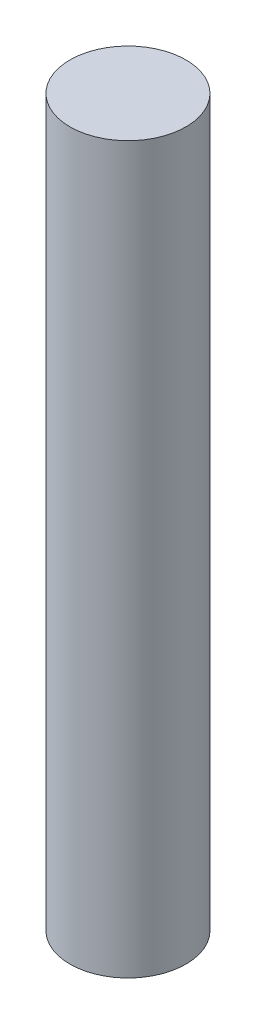
SolidWorks part; units mm, degrees
ref_plane "Front Plane" through (0, 0, 0) normal (0, 0, 1) x (1, 0, 0)
ref_plane "Top Plane" through (0, 0, 0) normal (0, 1, 0) x (1, 0, 0)
ref_plane "Right Plane" through (0, 0, 0) normal (1, 0, 0) x (0, 0, -1)
sketch "Sketch1" plane through (0, 0, 0) normal (0, 1, 0) x (1, 0, 0)
  circle A0 centre (0, 0) radius 3.048
  dimension "D1" = 6.096
extrude "Boss-Extrude1" add sketch "Sketch1" along normal blind 38.1
